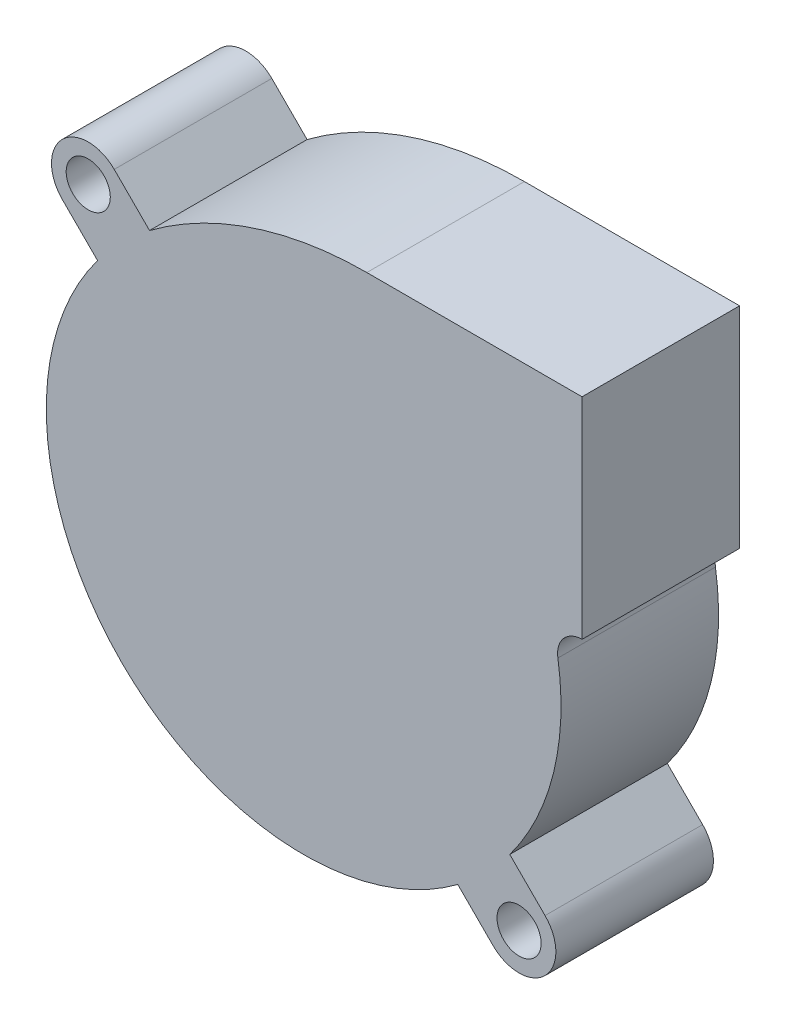
SolidWorks part; units mm, degrees
ref_plane "Front Plane" through (0, 0, 0) normal (0, 0, 1) x (1, 0, 0)
ref_plane "Top Plane" through (0, 0, 0) normal (0, 1, 0) x (1, 0, 0)
ref_plane "Right Plane" through (0, 0, 0) normal (1, 0, 0) x (0, 0, -1)
sketch "Sketch1" plane through (0, 0, 0) normal (0, 0, 1) x (1, 0, 0)
  line L0 (-20.5061, 20.5061) -> (20.5061, -20.5061) construction
  line L1 (-24.5, 0) -> (24.5, 0) construction
  line L2 (-22.981, 18.0312) -> (-19.6213, 14.6716)
  line L3 (22.981, -18.0312) -> (19.6213, -14.6716)
  line L4 (-14.6716, 19.6213) -> (-18.0312, 22.981)
  line L5 (14.6716, -19.6213) -> (18.0312, -22.981)
  line L7 (26.5, 26.5) -> (6.0145, 26.5)
  line L8 (26.5, 26.5) -> (26.5, 6.5)
  arc A0 (-19.6213, 14.6716) -> (14.6716, -19.6213) centre (0, 0) ccw
  circle A1 centre (-20.5061, 20.5061) radius 2.1
  circle A2 centre (20.5061, -20.5061) radius 2.1
  arc A3 (-18.0312, 22.981) -> (-22.981, 18.0312) centre (-20.5061, 20.5061) ccw
  arc A4 (18.0312, -22.981) -> (22.981, -18.0312) centre (20.5061, -20.5061) ccw
  arc A5 (19.6213, -14.6716) -> (24.2017, 3.8114) centre (0, 0) ccw
  arc A6 (26.5, 6.5) -> (24.2017, 3.8114) centre (26.5, 4.1734) ccw
  arc A7 (6.0145, 26.5) -> (-14.6716, 19.6213) centre (6.0145, -8.0437) ccw
  arc A8 (24.2017, 3.8114) -> (-14.6716, 19.6213) centre (0, 0) ccw construction
  point P20 (0, -24.5)
  dimension "D1" = 49
  dimension "D3" = 4.2
  dimension "D5" = 7
  dimension "D2" = 58
  dimension "D4" = 45
  dimension "D6" = 51
  dimension "D7" = 51
  dimension "D8" = 20
extrude "Boss-Extrude1" add sketch "Sketch1" along normal blind 15
